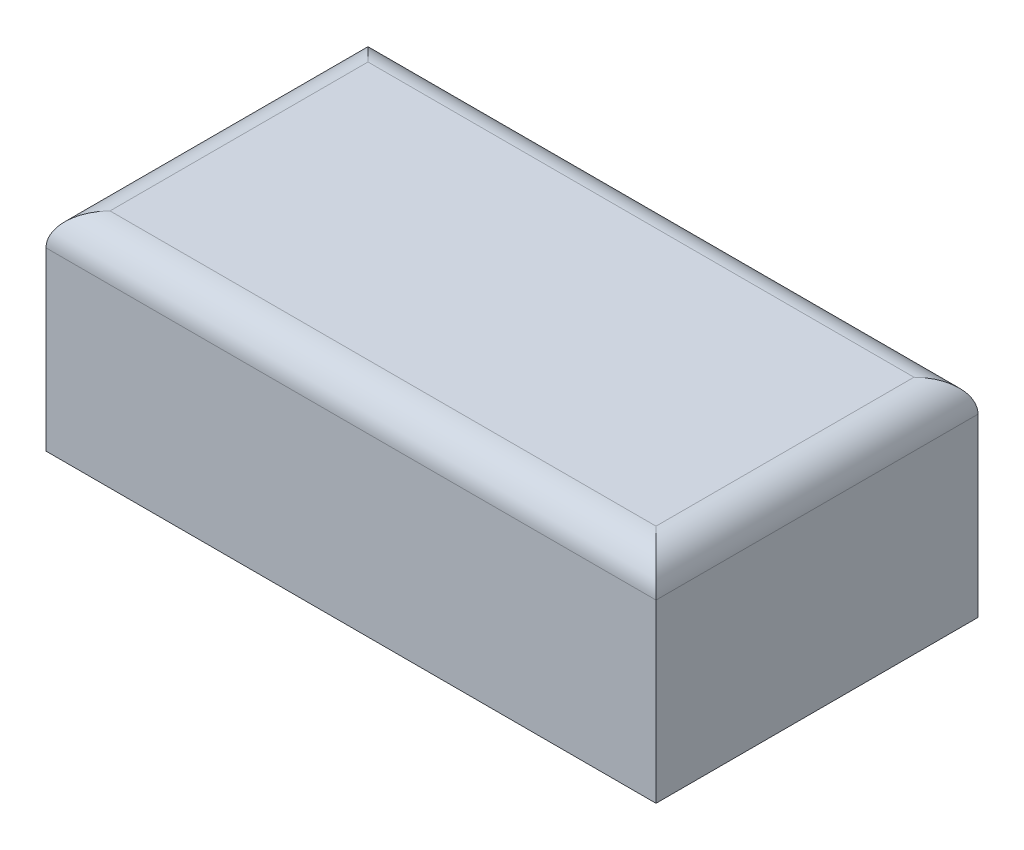
SolidWorks part; units mm, degrees
material "1060 Alloy"
ref_plane "Front Plane" through (0, 0, 0) normal (0, 0, 1) x (1, 0, 0)
ref_plane "Top Plane" through (0, 0, 0) normal (0, 1, 0) x (1, 0, 0)
ref_plane "Right Plane" through (0, 0, 0) normal (1, 0, 0) x (0, 0, -1)
sketch "Sketch1" plane through (0, 0, 0) normal (0, 1, 0) x (1, 0, 0)
  line L1 (953, 503) -> (-953, 503)
  line L2 (953, 503) -> (953, -503)
  line L3 (953, -503) -> (-953, -503)
  line L4 (-953, 503) -> (-953, -503)
  line L5 (953, 503) -> (-953, -503) construction
  line L6 (953, -503) -> (-953, 503) construction
  point P0 (0, 0)
  dimension "D1" = 1906
  dimension "D2" = 1006
extrude "Boss-Extrude1" add sketch "Sketch1" along normal blind 2 from offset 650
sketch "Sketch2" plane through (0, 650, 0) normal (0, -1, 0) x (1, 0, 0)
  line L1 (953, 503) -> (-953, 503)
  line L2 (953, 503) -> (953, -503)
  line L3 (953, -503) -> (-953, -503)
  line L4 (-953, 503) -> (-953, -503)
  line L5 (953, 503) -> (-953, -503) construction
  line L6 (953, -503) -> (-953, 503) construction
  line L7 (950, 501.4166) -> (-950, 501.4166)
  line L8 (950, 501.4166) -> (950, -501.4166)
  line L9 (950, -501.4166) -> (-950, -501.4166)
  line L10 (-950, 501.4166) -> (-950, -501.4166)
  line L11 (950, 501.4166) -> (-950, -501.4166) construction
  line L12 (950, -501.4166) -> (-950, 501.4166) construction
  point P0 (0, 0)
  point P7 (0, 0)
  dimension "D1" = 1900
extrude "Boss-Extrude2" add sketch "Sketch2" along normal blind 648
fillet "Fillet1" radius 100 8 edges at (0, 652, -503) (-953, 652, 0) (0, 652, 503) (950, 650, 0) (953, 652, 0) (0, 650, 501.4166) (0, 650, -501.4166) (-950, 650, 0)
sketch "Sketch3" plane through (0, 0, -503) normal (0, 0, -1) x (-1, 0, 0)
  line L0 (953, 2) -> (-953, 2) construction
  line L1 (700, 282) -> (-700, 282)
  line L2 (700, 282) -> (700, -278)
  line L3 (700, -278) -> (-700, -278)
  line L4 (-700, 282) -> (-700, -278)
  line L5 (700, 282) -> (-700, -278) construction
  line L6 (700, -278) -> (-700, 282) construction
  point P0 (0, 2)
  dimension "D1" = 560
  dimension "D2" = 1400
extrude "Cut-Extrude1" cut sketch "Sketch3" against normal blind 143
